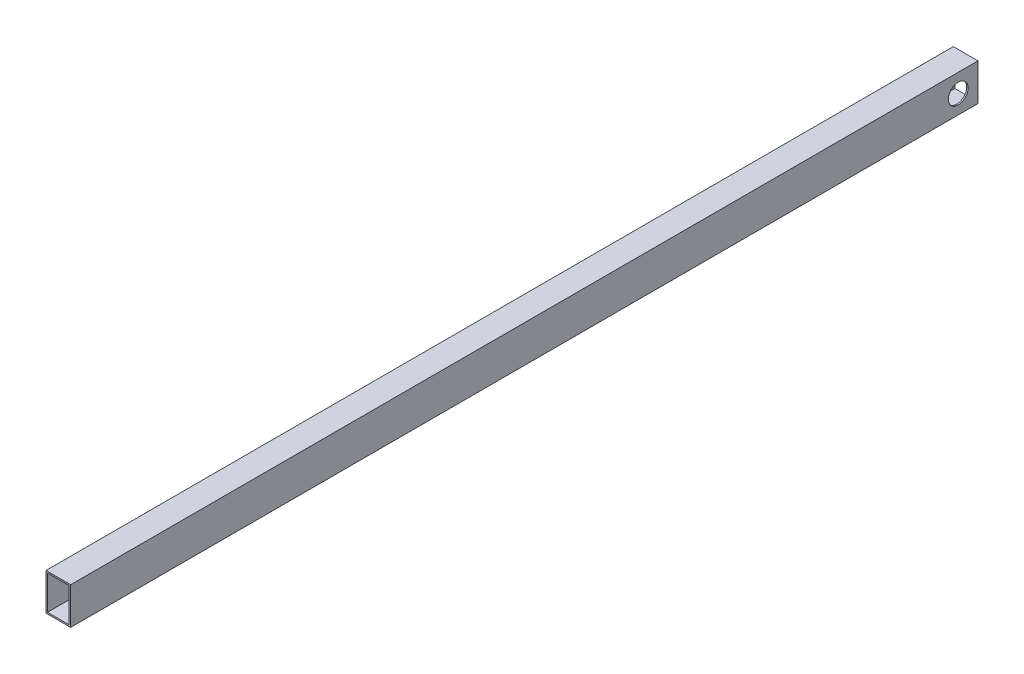
SolidWorks part; units mm, degrees
material "Plain Carbon Steel"
ref_plane "Front Plane" through (0, 0, 0) normal (0, 0, 1) x (1, 0, 0)
ref_plane "Top Plane" through (0, 0, 0) normal (0, 1, 0) x (1, 0, 0)
ref_plane "Right Plane" through (0, 0, 0) normal (1, 0, 0) x (0, 0, -1)
sketch "Sketch1" plane through (0, 0, 0) normal (0, 0, 1) x (1, 0, 0)
  line B0 (-50, -75) -> (50, -75)
  line B1 (-50, -75) -> (-50, 75)
  line B2 (50, -75) -> (50, 75)
  line B3 (-50, 75) -> (50, 75)
  line B4 (-44, -69) -> (44, -69)
  line B5 (-44, -69) -> (-44, 69)
  line B6 (44, -69) -> (44, 69)
  line B7 (-44, 69) -> (44, 69)
sketch_block_instance "15x10x6_profil-1"
sketch_block "15x10x6_profil" parameters "D1"=100, "D2"=150, "D3"=6, "D4"=6
extrude "Boss-Extrude1" add sketch "Sketch1" along normal blind 3600 and the other way blind 80
sketch "Sketch2" plane through (0, 0, 0) normal (1, 0, 0) x (0, 0, -1)
  circle A0 centre (0, 0) radius 40
  dimension "D1" = 80
extrude "Cut-Extrude1" cut sketch "Sketch2" against normal through all and the other way through all
sketch "Sketch3" plane through (-50, 0, 0) normal (-1, 0, 0) x (0, 0, 1)
  line L1 (0, 75) -> (-80, 75)
  line L2 (-80, 75) -> (-80, -75)
  line L3 (-80, -75) -> (0, -75)
  arc A0 (0, 75) -> (0, -75) centre (0, 0) ccw
extrude "Cut-Extrude2" [suppressed] cut sketch "Sketch3" against normal through all
sketch "Sketch4" plane through (-50, 0, 0) normal (-1, 0, 0) x (0, 0, 1)
  point P0 (0, 0)
